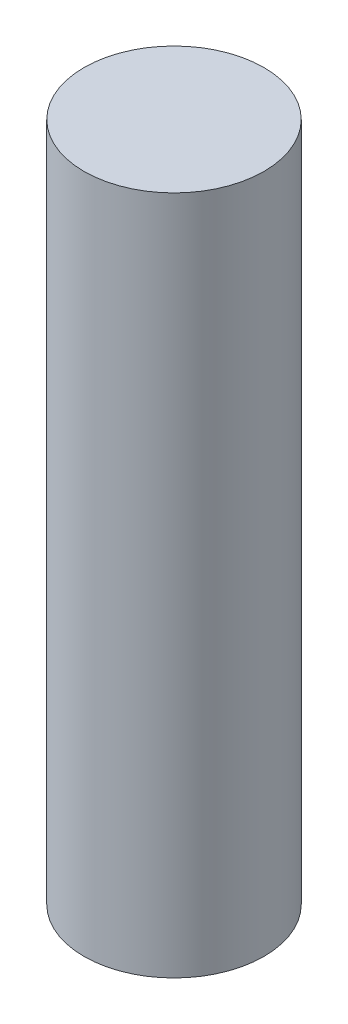
SolidWorks part; units mm, degrees
ref_plane "前视基准面" through (0, 0, 0) normal (0, 0, 1) x (1, 0, 0)
ref_plane "上视基准面" through (0, 0, 0) normal (0, 1, 0) x (1, 0, 0)
ref_plane "右视基准面" through (0, 0, 0) normal (1, 0, 0) x (0, 0, -1)
sketch "草图1" plane through (0, 0, 0) normal (0, 0, 1) x (1, 0, 0)
  line L0 (79, 68) -> (70, 68)
  line L1 (70, 68) -> (70, 0)
  line L2 (70, 0) -> (79, 0)
  line L3 (79, 0) -> (79, 68)
  line L4 (70, 68) -> (70, 0) construction
revolve "旋转1" add sketch "草图1" angle 360 about L4
